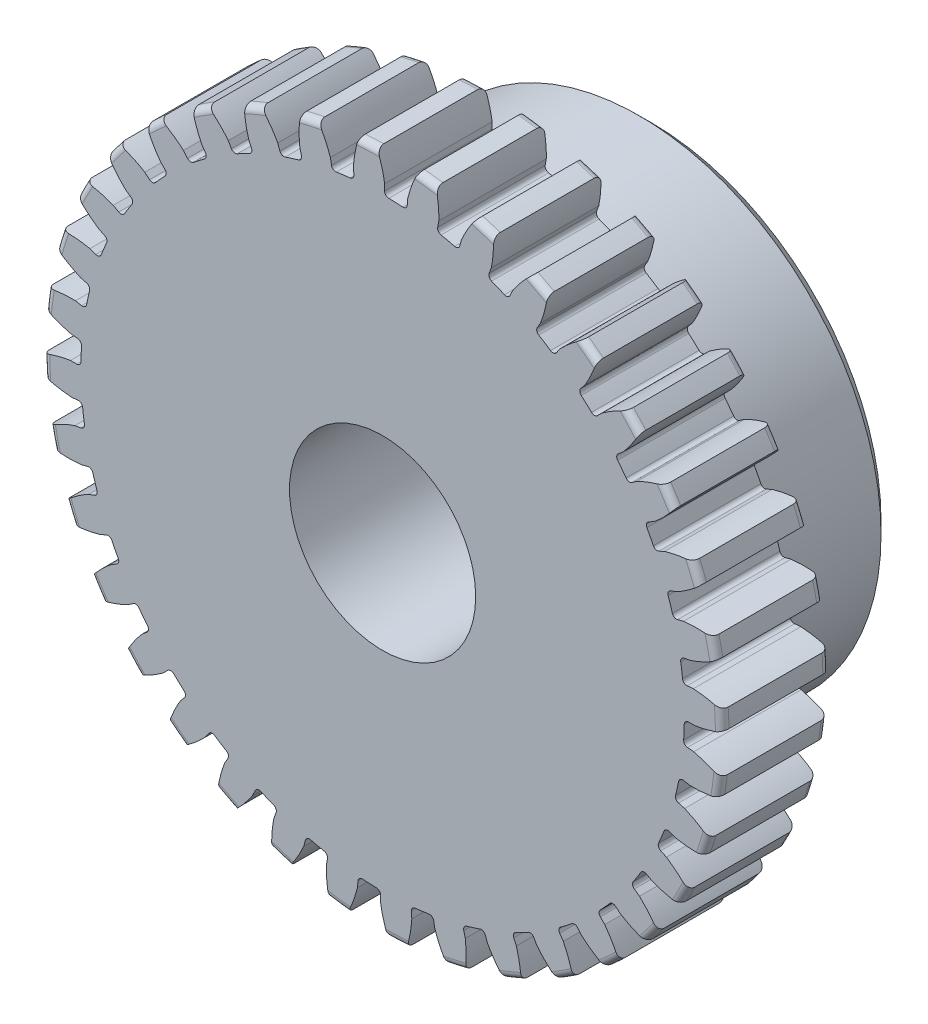
SolidWorks part; units mm, degrees
material "AISI 1020"
ref_plane "Front" through (0, 0, 0) normal (0, 0, 1) x (1, 0, 0)
ref_plane "Top" through (0, 0, 0) normal (0, 1, 0) x (1, 0, 0)
ref_plane "Right" through (0, 0, 0) normal (1, 0, 0) x (0, 0, -1)
sketch "Sketch1" plane through (0, 0, 0) normal (0, 0, 1) x (1, 0, 0)
  line L0 (-457.2, 0) -> (457.2, 0) construction
  circle A0 centre (0, 0) radius 20.066
  circle A1 centre (0, 0) radius 19.05 construction
  circle A3 centre (0, 0) radius 17.8255 construction
  dimension "D1" = 1.2245
  dimension "D2" = 2.2405
extrude "Boss-Extrude1" add sketch "Sketch1" against normal blind 6.35
sketch "Sketch2" plane through (0, 0, 0) normal (1, 0, 0) x (0, 0, -1)
  line L0 (6.35, 0) -> (15.875, 0)
  line L1 (6.35, 0) -> (6.35, 14.2875)
  line L2 (6.35, 14.2875) -> (15.875, 14.2875)
  line L3 (15.875, 14.2875) -> (15.875, 0)
  point P5 (15.875, -14.2875)
revolve "Revolve1" add sketch "Sketch2" angle 360 mid plane about L0
fillet "Fillet2" radius 0.4013 3 edges at (20.066, 0, -6.35) (20.066, 0, 0) (14.2875, 0, -6.35)
sketch "Sketch3" plane through (0, 0, 0) normal (0, 0, 1) x (1, 0, 0)
  line L0 (0, 0) -> (0, 20.066) construction
  line L1 (-4.6178, 17.8558) -> (0, 19.05)
  line L2 (-9.5921, 19.05) -> (9.5921, 19.05) construction
  line L3 (-9.2865, 16.6483) -> (9.2865, 21.4517) construction
  line L4 (-4.6178, 17.8558) -> (0, 0) construction
  line L5 (-11.4075, 14.4921) -> (0, 0) construction
  line L6 (-11.4075, 14.4921) -> (-1.663, 22.1626) construction
  line L7 (-3.22, 18.16) -> (0, 0) construction
  line L8 (-3.22, 18.16) -> (0.0676, 18.7429) construction
  arc A0 (-4.6178, 17.8558) -> (-11.4075, 14.4921) centre (0, 0) ccw
  circle A1 centre (0, 0) radius 19.05 construction
  circle A2 centre (0, 0) radius 18.4432 construction
  arc A3 (-4.6178, 17.8558) -> (-3.22, 18.16) centre (0, 0) cw
  circle A4 centre (0, 0) radius 20.066 construction
  point P6 (0, 19.05)
  dimension "D1" = 4.7697
  dimension "D3" = 12.4013
  dimension "D5" = 3.3388
  dimension "D2" = 7.6316
  dimension "D4" = 1.4309
sketch "Sketch4" plane through (0, 0, 0) normal (0, 0, 1) x (1, 0, 0)
  line L0 (0, 0) -> (0.8302, 19.0138) construction
  line L1 (0.1199, 18.4428) -> (0.1199, 17.8251)
  line L2 (0, 19.05) -> (1.6603, 18.9775) construction
  line L3 (1.488, 18.3831) -> (1.4342, 17.7677)
  line L4 (0.1199, 17.8251) -> (0, 0) construction
  line L5 (0, 0) -> (0, 20.066) construction
  arc A0 (1.4342, 17.7677) -> (0.1199, 17.8251) centre (0, 0) ccw
  arc A1 (0, 19.05) -> (1.6603, 18.9775) centre (0, 0) cw construction
  circle A2 centre (0, 0) radius 19.05 construction
  circle A3 centre (0, 0) radius 18.4432 construction
  circle A4 centre (0, 0) radius 17.8255 construction
  arc A5 (3.5883, 21.9333) -> (-1.663, 22.1626) centre (0, 0) ccw
  spline S0 degree 2 poles (-1.663, 22.1626) (-0.1927, 20.4949) (0.1199, 18.4428) knots 0 0 0 1 1 1
  spline S1 degree 2 poles (3.5883, 21.9333) (1.9782, 20.4001) (1.488, 18.3831) knots 0 0 0 1 1 1
  dimension "D1" = 1.6624
extrude "Cut-Extrude1" cut sketch "Sketch4" against normal through all
fillet "Fillet1" radius 0.2494 2 edges at (1.4342, 17.7677, -3.175) (0.1199, 17.8251, -3.175)
pattern_circular "CirPattern1" count 36 over 360 about axis through (0, 0, -6.35) along (0, 0, 1) of "Cut-Extrude1", "Fillet1"
sketch "Sketch5" plane through (0, 0, 0) normal (0, 0, 1) x (1, 0, 0)
  circle A0 centre (0, 0) radius 4.7625
  circle A1 centre (0, 0) radius 7.9375 construction
  dimension "Bore Min" = 9.525
  dimension "Bore Max" = 15.875
extrude "Cut-Extrude2" cut sketch "Sketch5" against normal through all
chamfer "Chamfer1" distance 0.7144 angle 45 3 edges at (14.2875, 0, -15.875) (4.7625, 0, 0) (4.7625, 0, -15.875)
sketch "Pitch Dia" plane through (0, 0, 0) normal (0, 0, 1) x (1, 0, 0)
  circle A0 centre (0, 0) radius 19.05 construction
  circle A1 centre (0, 0) radius 19.05
sketch "Sketch6" plane through (0, 0, 0) normal (0, 0, 1) x (1, 0, 0)
  circle A0 centre (0, 0) radius 5.5
  dimension "D1" = 11
extrude "Cut-Extrude3" cut sketch "Sketch6" against normal through all
equation "\"D1@Boss-Extrude1\" = \"Face Wd@Sketch2\""
equation "\"D2@Sketch3\" = \"D1@Sketch3\"*1.6"
equation "\"D3@Sketch3\" = \"D1@Sketch3\"+\"D2@Sketch3\""
equation "\"D4@Sketch3\" = \"D1@Sketch3\"*.3"
equation "\"D5@Sketch3\" = \"D1@Sketch3\"-\"D4@Sketch3\""
equation "\"D1@Sketch4\" = 1.5708/(\"Number of Teeth@Sketch1\"/\"Ptich Dia@Sketch1\")"
equation "\"D1@Chamfer1\" = \"B Hub Dia@Sketch2\"*.025"
equation "\"D1@CirPattern1\" = \"Number of Teeth@Sketch1\""
equation "\"D1@Fillet1\" = \"D1@Sketch4\"*.15"
equation "\"D1@Fillet2\" = \"OD@Sketch1\"*.01"
equation "\"D1@Sketch1\" = 1.157/(\"Number of Teeth@Sketch1\"/\"Ptich Dia@Sketch1\")"
